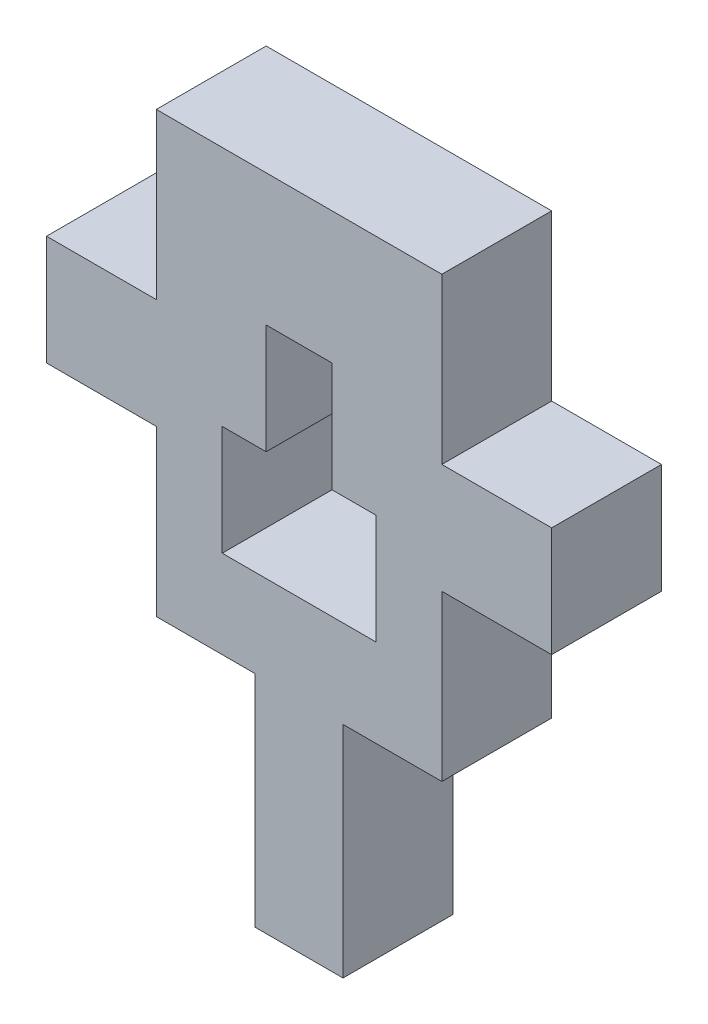
SolidWorks part; units mm, degrees
ref_plane "Plan de face" through (0, 0, 0) normal (0, 0, 1) x (1, 0, 0)
ref_plane "Plan de dessus" through (0, 0, 0) normal (0, 1, 0) x (1, 0, 0)
ref_plane "Plan de droite" through (0, 0, 0) normal (1, 0, 0) x (0, 0, -1)
sketch "Esquisse1" plane through (0, 0, 0) normal (0, 0, 1) x (1, 0, 0)
  line L1 (0, 0) -> (13, 0)
  line L2 (0, 0) -> (0, 20)
  line L3 (0, 20) -> (13, 20)
  line L4 (13, 0) -> (13, 20)
  line L5 (13, 7.5) -> (18, 7.5)
  line L6 (13, 7.5) -> (13, 12.5)
  line L7 (13, 12.5) -> (18, 12.5)
  line L8 (18, 7.5) -> (18, 12.5)
  line L9 (4.5, 0) -> (8.5, 0)
  line L10 (4.5, 0) -> (4.5, -10)
  line L11 (4.5, -10) -> (8.5, -10)
  line L12 (8.5, 0) -> (8.5, -10)
  line L13 (0, 12.5) -> (-5, 12.5)
  line L14 (0, 12.5) -> (0, 7.5)
  line L15 (0, 7.5) -> (-5, 7.5)
  line L16 (-5, 12.5) -> (-5, 7.5)
  dimension "D1" = 20
  dimension "D2" = 13
  dimension "D3" = 7.5
  dimension "D4" = 5
  dimension "D5" = 5
  dimension "D6" = 10
  dimension "D7" = 4
  dimension "D8" = 4.5
  dimension "D9" = 5
  dimension "D10" = 5
  dimension "D11" = 7.5
extrude "Boss.-Extru.1" add sketch "Esquisse1" along normal blind 5 contours L12 L1 L10 L11 | L13 L16 L15 L2 | L1 L4 L3 L2 | L5 L8 L7 L4
sketch "Esquisse2" plane through (0, 0, 0) normal (0, 0, -1) x (-1, 0, 0)
  line L0 (0, 0) -> (-4.5, 0) construction
  line L1 (-10, 4) -> (-3, 4)
  line L2 (-10, 4) -> (-10, 9)
  line L3 (-10, 9) -> (-3, 9)
  line L4 (-3, 4) -> (-3, 9)
  line L5 (-13, 0) -> (-13, 7.5) construction
  dimension "D1" = 7
  dimension "D2" = 5
  dimension "D3" = 9
  dimension "D4" = 3
extrude "Enlèv. mat.-Extru.1" cut sketch "Esquisse2" against normal blind 10
sketch "Esquisse3" plane through (0, 0, 0) normal (0, 0, -1) x (-1, 0, 0)
  line L0 (-10, 4) -> (-3, 4) construction
  line L1 (-8, 4) -> (-5, 4)
  line L2 (-8, 4) -> (-8, 14)
  line L3 (-8, 14) -> (-5, 14)
  line L4 (-5, 4) -> (-5, 14)
  line L5 (-10, 9) -> (-10, 4) construction
  dimension "D1" = 3
  dimension "D2" = 10
  dimension "D3" = 2
extrude "Enlèv. mat.-Extru.2" cut sketch "Esquisse3" against normal blind 10
